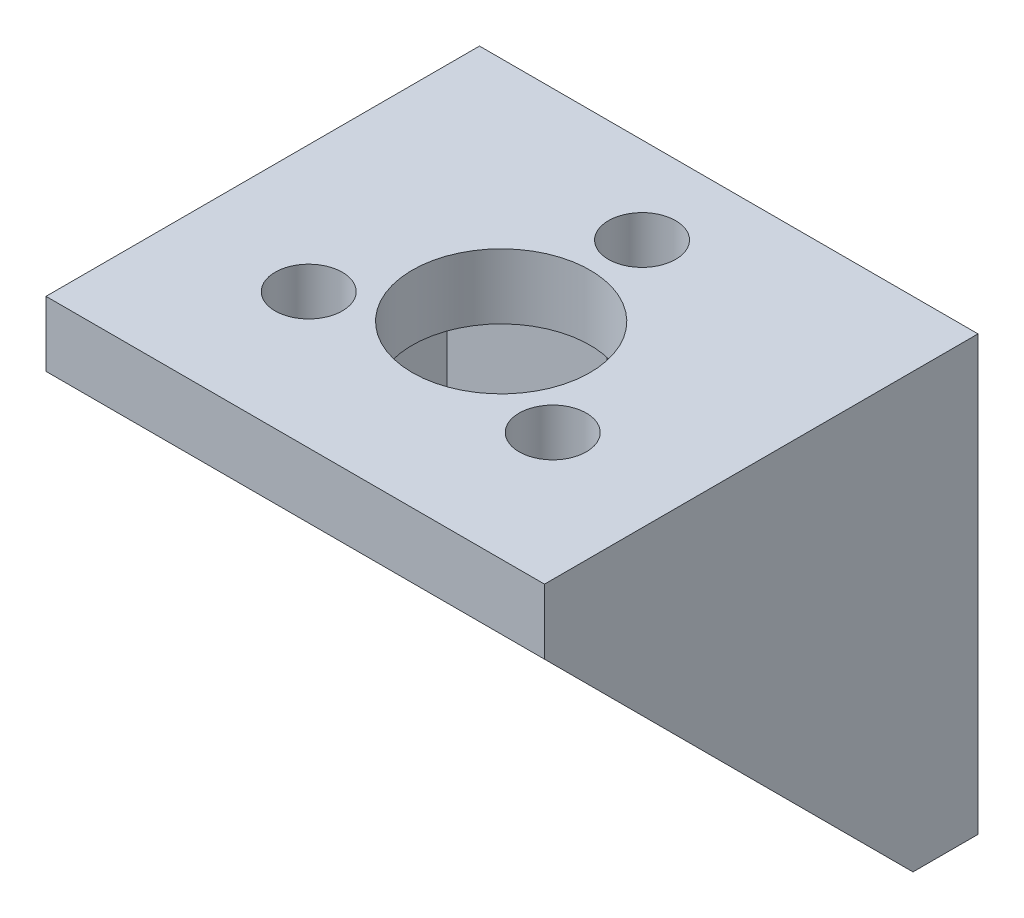
SolidWorks part; units mm, degrees
material "1060 Alloy"
ref_plane "Front Plane" through (0, 0, 0) normal (0, 0, 1) x (1, 0, 0)
ref_plane "Top Plane" through (0, 0, 0) normal (0, 1, 0) x (1, 0, 0)
ref_plane "Right Plane" through (0, 0, 0) normal (1, 0, 0) x (0, 0, -1)
sketch "Sketch1" plane through (0, 0, 0) normal (1, 0, 0) x (0, 0, -1)
  line L0 (0, 0) -> (-20, 0)
  line L1 (-20, 0) -> (-20, -3)
  line L2 (-20, -3) -> (-11.5, -11.5)
  line L3 (-11.5, -11.5) -> (0, 0) construction
  line L4 (-3, -20) -> (-11.5, -11.5)
  line L5 (0, -20) -> (-3, -20)
  line L6 (0, 0) -> (0, -20)
  dimension "D1" = 3
  dimension "D2" = 20
extrude "Boss-Extrude1" add sketch "Sketch1" along normal mid plane 23
sketch "Sketch2" plane through (0, 0, 0) normal (1, 0, 0) x (0, 0, -1)
  line L0 (-20, -3) -> (-3, -20) construction
  line L1 (-3, -3) -> (-20, -3)
  line L2 (-3, -3) -> (-3, -20)
  line L3 (-3, -20) -> (-20, -20)
  line L4 (-20, -3) -> (-20, -20)
  line L5 (-20, 0) -> (-20, -3) construction
extrude "Cut-Extrude1" cut sketch "Sketch2" against normal mid plane 20
sketch "Sketch3" plane through (0, 0, 3) normal (0, 0, 1) x (1, 0, 0)
  line L0 (0, -9) -> (0, -12) construction
  line L1 (-3, -9) -> (-3, -12)
  line L2 (3, -9) -> (3, -12)
  line L3 (0, -10.5) -> (0.7454, -10.5) construction
  line L4 (-10, -20) -> (10, -20) construction
  arc A0 (-3, -9) -> (3, -9) centre (0, -9) cw
  arc A1 (-3, -12) -> (3, -12) centre (0, -12) ccw
  dimension "D3" = 9
  dimension "D4" = 5
  dimension "D1" = 3
  dimension "D2" = 3
extrude "Cut-Extrude2" cut sketch "Sketch3" against normal up to next
sketch "Esboço1" plane through (0, 0, 0) normal (0, 1, 0) x (1, 0, 0)
  circle A2 centre (0, -10.5) radius 4.1
  dimension "D1" = 8.2
extrude "Corte-extrusão1" cut sketch "Esboço1" against normal up to next
sketch "Esboço3" plane through (0, -3, 0) normal (0, -1, 0) x (1, 0, 0)
  line L4 (10, 3) -> (10, 20)
  line L5 (10, 20) -> (-10, 20)
  line L6 (-10, 20) -> (-10, 3)
  line L7 (-10, 3) -> (10, 3)
  line L8 (10, 3) -> (10, 20)
  line L9 (10, 20) -> (-10, 20)
  line L10 (-10, 20) -> (-10, 3)
  line L11 (-10, 3) -> (10, 3)
  line L32 (0, 14.7) -> (-2.4249, 14.7)
  line L33 (-2.4249, 14.7) -> (-3.6373, 12.6)
  line L34 (-3.6373, 12.6) -> (-4.8497, 10.5)
  line L35 (-4.8497, 10.5) -> (-3.6373, 8.4)
  line L36 (-3.6373, 8.4) -> (-2.4249, 6.3)
  line L37 (-2.4249, 6.3) -> (0, 6.3)
  line L38 (0, 6.3) -> (2.4249, 6.3)
  line L39 (2.4249, 6.3) -> (3.6373, 8.4)
  line L40 (3.6373, 8.4) -> (4.8497, 10.5)
  line L41 (4.8497, 10.5) -> (3.6373, 12.6)
  line L42 (3.6373, 12.6) -> (2.4249, 14.7)
  line L43 (2.4249, 14.7) -> (0, 14.7)
  dimension "D1" = 0
extrude "Corte-extrusão2" [suppressed] cut sketch "Esboço3" against normal blind 1.5 contours L32 L33 L34 L35 L36 L37 L38 L39 L40 L41 L42 L43
sketch "Esboço6" plane through (0, 0, 0) normal (0, 1, 0) x (1, 0, 0)
  circle A0 centre (0, -10.5) radius 6.5 construction
  circle A3 centre (0, -4) radius 1.55
  dimension "D1" = 3.1
  dimension "D2" = 13
extrude "Corte-extrusão5" cut sketch "Esboço6" against normal through all
pattern_circular "PadrãoCircular2" count 3 over 360 about axis through (0, 0, 10.5) along (0, 1, 0) of "Corte-extrusão5"
sketch "Esboço11" plane through (0, -3, 0) normal (0, -1, 0) x (1, 0, 0)
  circle A0 centre (0, 4) radius 2.8
  dimension "D1" = 5.6
extrude "Corte-extrusão8" cut sketch "Esboço11" along normal through all
